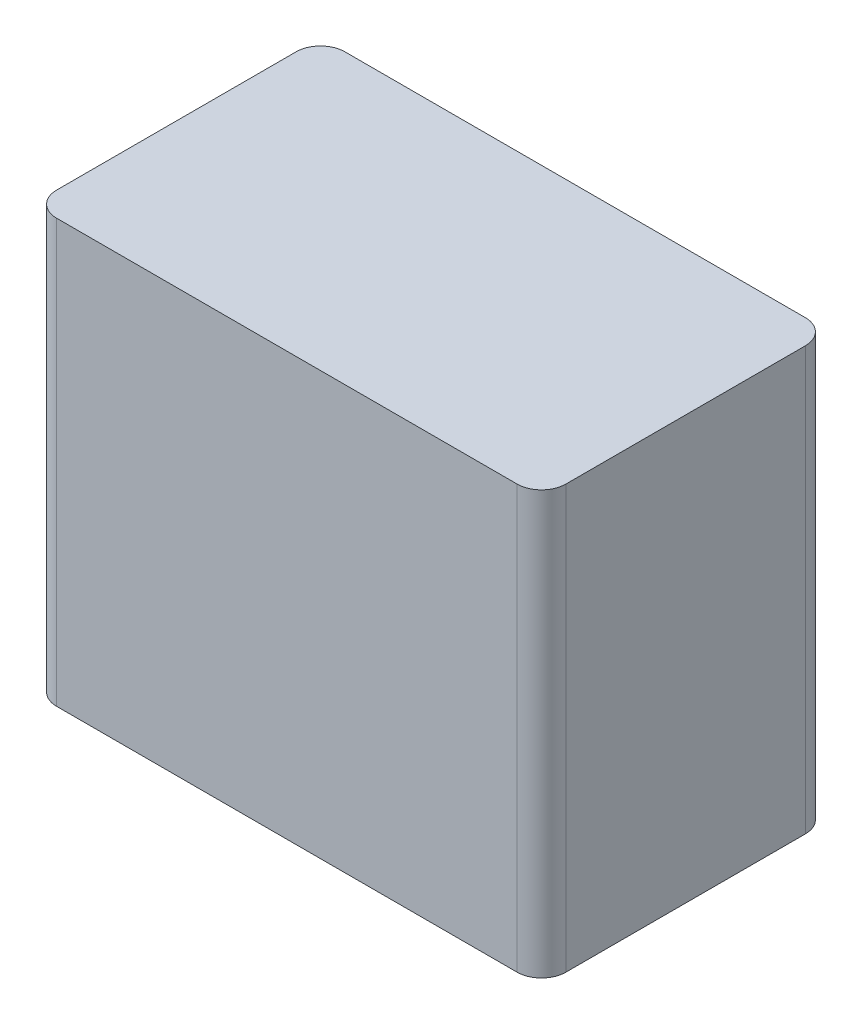
SolidWorks part; units mm, degrees
ref_plane "Front Plane" through (0, 0, 0) normal (0, 0, 1) x (1, 0, 0)
ref_plane "Top Plane" through (0, 0, 0) normal (0, 1, 0) x (1, 0, 0)
ref_plane "Right Plane" through (0, 0, 0) normal (1, 0, 0) x (0, 0, -1)
sketch "Sketch1" plane through (0, 0, 0) normal (0, 0, 1) x (1, 0, 0)
  line L1 (0, 0) -> (-53, 0)
  line L2 (0, 0) -> (0, 44)
  line L3 (0, 44) -> (-53, 44)
  line L4 (-53, 0) -> (-53, 44)
  dimension "D1" = 53
  dimension "D2" = 44
extrude "Boss-Extrude1" add sketch "Sketch1" along normal blind 30
fillet "Fillet1" radius 2.54 4 edges at (-53, 22, 0) (-53, 22, 30) (0, 22, 0) (0, 22, 30)
